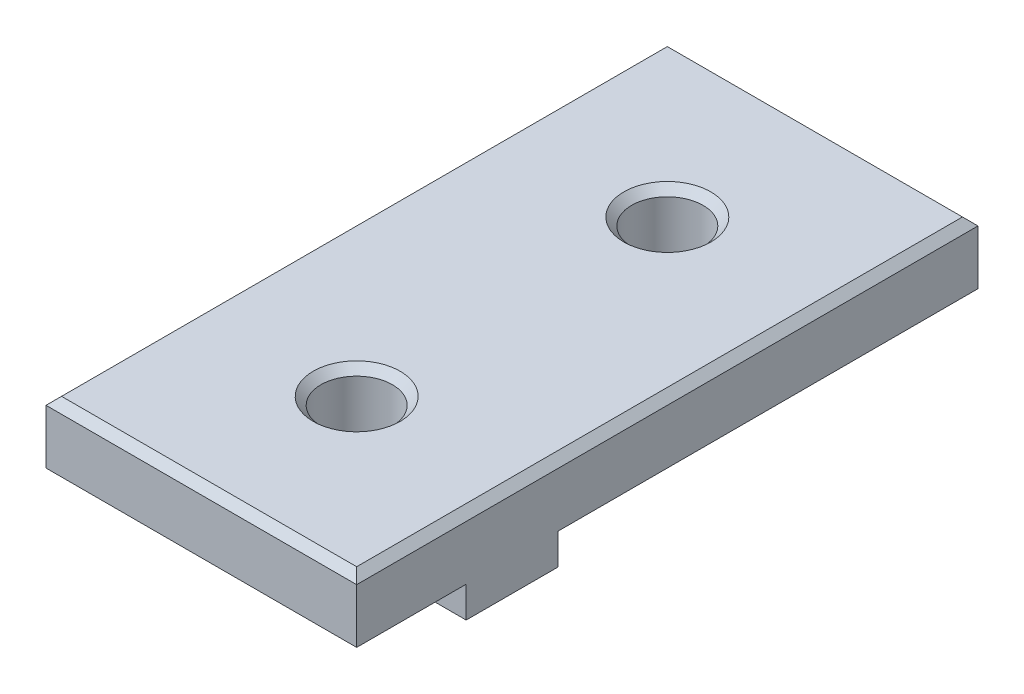
SolidWorks part; units mm, degrees
ref_plane "Plano frontal" through (0, 0, 0) normal (0, 0, 1) x (1, 0, 0)
ref_plane "Plano superior" through (0, 0, 0) normal (0, 1, 0) x (1, 0, 0)
ref_plane "Plano direito" through (0, 0, 0) normal (1, 0, 0) x (0, 0, -1)
sketch "Esboço1" plane through (0, 0, 0) normal (0, 1, 0) x (1, 0, 0)
  line L1 (-10, 20) -> (10, 20)
  line L2 (-10, 20) -> (-10, -20)
  line L3 (-10, -20) -> (10, -20)
  line L4 (10, 20) -> (10, -20)
  line L5 (-10, 20) -> (10, -20) construction
  line L6 (-10, -20) -> (10, 20) construction
  point P0 (0, 0)
  dimension "D1" = 20
  dimension "D2" = 40
extrude "Ressalto-extrusão1" add sketch "Esboço1" along normal blind 4
sketch "Esboço2" plane through (0, 4, 0) normal (0, 1, 0) x (1, 0, 0)
  line L0 (-10, 0) -> (10, 0) construction
  line L1 (-10, -20) -> (10, -20) construction
  line L2 (10, -20) -> (10, 20) construction
  line L5 (-10, 20) -> (-10, -20) construction
  line L6 (10, -20) -> (10, 20) construction
  line L7 (10, 20) -> (-10, 20) construction
  circle A0 centre (0, 10) radius 2.3
  circle A1 centre (0, -10) radius 2.3
  dimension "D1" = 4.6
  dimension "D2" = 4.6
  dimension "D3" = 10
  dimension "D4" = 10
  dimension "D5" = 10
extrude "Corte-extrusão1" cut sketch "Esboço2" against normal through all both and the other way through all
sketch "Esboço3" plane through (0, 0, 0) normal (0, -1, 0) x (1, 0, 0)
  line L0 (-10, 0) -> (10, 0) construction
  line L1 (-2.95, -7) -> (2.95, -7)
  line L2 (-2.95, -7) -> (-2.95, -1)
  line L3 (-2.95, -1) -> (2.95, -1)
  line L4 (2.95, -7) -> (2.95, -1)
  line L5 (-2.95, -7) -> (2.95, -1) construction
  line L6 (-2.95, -1) -> (2.95, -7) construction
  line L7 (-2.95, -13) -> (2.95, -13)
  line L8 (-2.95, -13) -> (-2.95, -20)
  line L9 (-2.95, -20) -> (2.95, -20)
  line L10 (2.95, -13) -> (2.95, -20)
  line L11 (-2.95, -13) -> (2.95, -20) construction
  line L12 (-2.95, -20) -> (2.95, -13) construction
  line L13 (-10, 12.95) -> (-3, 12.95)
  line L14 (-10, 12.95) -> (-10, 7.05)
  line L15 (-10, 7.05) -> (-3, 7.05)
  line L16 (-3, 12.95) -> (-3, 7.05)
  line L17 (-10, 12.95) -> (-3, 7.05) construction
  line L18 (-10, 7.05) -> (-3, 12.95) construction
  line L19 (3, 12.95) -> (10, 12.95)
  line L20 (3, 12.95) -> (3, 7.05)
  line L21 (3, 7.05) -> (10, 7.05)
  line L22 (10, 12.95) -> (10, 7.05)
  line L23 (3, 12.95) -> (10, 7.05) construction
  line L24 (3, 7.05) -> (10, 12.95) construction
  line L26 (-10, -20) -> (-10, 20) construction
  line L29 (10, 20) -> (10, -20) construction
  line L30 (10, -20) -> (-10, -20) construction
  circle A1 centre (0, -10) radius 2.3 construction
  circle A2 centre (0, 10) radius 2.3 construction
  point P0 (0, -4)
  point P5 (0, -16.5)
  point P10 (-6.5, 10)
  point P15 (6.5, 10)
  point P20 (0, 10)
  point P23 (0, -10)
  point P28 (0, -13)
  dimension "D2" = 5.9
  dimension "D3" = 5.9
  dimension "D4" = 5.9
  dimension "D5" = 5.9
  dimension "D6" = 1
  dimension "D1" = 3
  dimension "D7" = 3
  dimension "D8" = 3
  dimension "D9" = 3
extrude "Ressalto-extrusão2" add sketch "Esboço3" along normal blind 2
chamfer "Chanfro1" distance 0.5 angle 45 6 edges at (0, 4, 20) (-10, 4, 0) (0, 4, -20) (10, 4, 0) (0, 4, -7.7) (0, 4, 12.3)
equation "\"D3@Esboço3\"=\"D2@Esboço3\""
equation "\"D4@Esboço3\"=\"D2@Esboço3\""
equation "\"D5@Esboço3\"=\"D2@Esboço3\""
equation "\"D1@Esboço2\"=\"D2@Esboço2\""
equation "\"D7@Esboço3\"=\"D1@Esboço3\""
equation "\"D8@Esboço3\"=\"D1@Esboço3\""
equation "\"D9@Esboço3\"=\"D1@Esboço3\""
